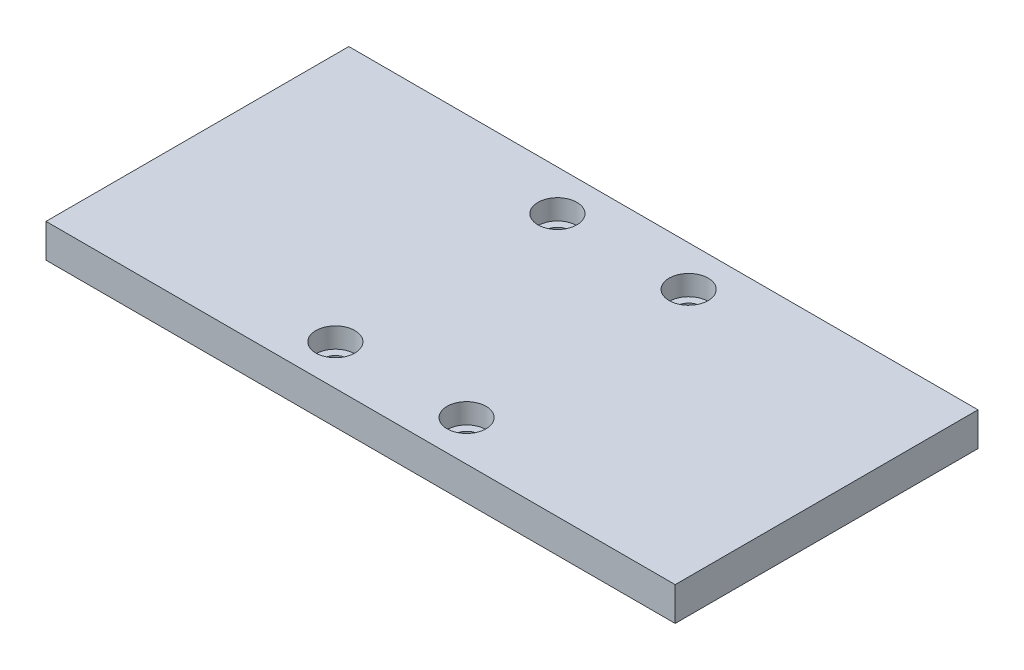
SolidWorks part; units mm, degrees
ref_plane "Front Plane" through (0, 0, 0) normal (0, 0, 1) x (1, 0, 0)
ref_plane "Top Plane" through (0, 0, 0) normal (0, 1, 0) x (1, 0, 0)
ref_plane "Right Plane" through (0, 0, 0) normal (1, 0, 0) x (0, 0, -1)
sketch "Sketch1" plane through (0, 0, 0) normal (0, 1, 0) x (1, 0, 0)
  line L1 (46.75, -22.5) -> (-46.75, -22.5)
  line L2 (46.75, -22.5) -> (46.75, 22.5)
  line L3 (46.75, 22.5) -> (-46.75, 22.5)
  line L4 (-46.75, -22.5) -> (-46.75, 22.5)
  line L5 (46.75, -22.5) -> (-46.75, 22.5) construction
  line L6 (46.75, 22.5) -> (-46.75, -22.5) construction
  point P0 (0, 0)
  dimension "D1" = 45
  dimension "D2" = 93.5
extrude "Boss-Extrude1" add sketch "Sketch1" along normal blind 5
sketch "Sketch2" plane through (0, 5, 0) normal (0, 1, 0) x (1, 0, 0)
  line L0 (0, 21.9895) -> (0, -22.7055) construction
  line L1 (-46.75, -22.5) -> (46.75, -22.5) construction
  line L4 (46.75, 22.5) -> (-46.75, 22.5) construction
  circle A1 centre (-9.75, -16.5) radius 1.75
  circle A2 centre (-9.75, 16.5) radius 1.75
  circle A3 centre (9.75, -16.5) radius 1.75
  circle A4 centre (9.75, 16.5) radius 1.75
  dimension "D1" = 6
  dimension "D2" = 6
  dimension "D3" = 9.75
  dimension "D4" = 9.75
  dimension "D5" = 3.5
  dimension "D6" = 3.5
extrude "Cut-Extrude1" cut sketch "Sketch2" against normal through all both and the other way through all
sketch "Sketch3" plane through (0, 5, 0) normal (0, 1, 0) x (1, 0, 0)
  circle A0 centre (-9.75, 16.5) radius 2.9
  circle A1 centre (9.75, 16.5) radius 2.9
  circle A2 centre (9.75, -16.5) radius 2.9
  circle A3 centre (-9.75, -16.5) radius 2.9
  dimension "D1" = 5.8
extrude "Cut-Extrude2" cut sketch "Sketch3" against normal blind 3 and the other way through all
